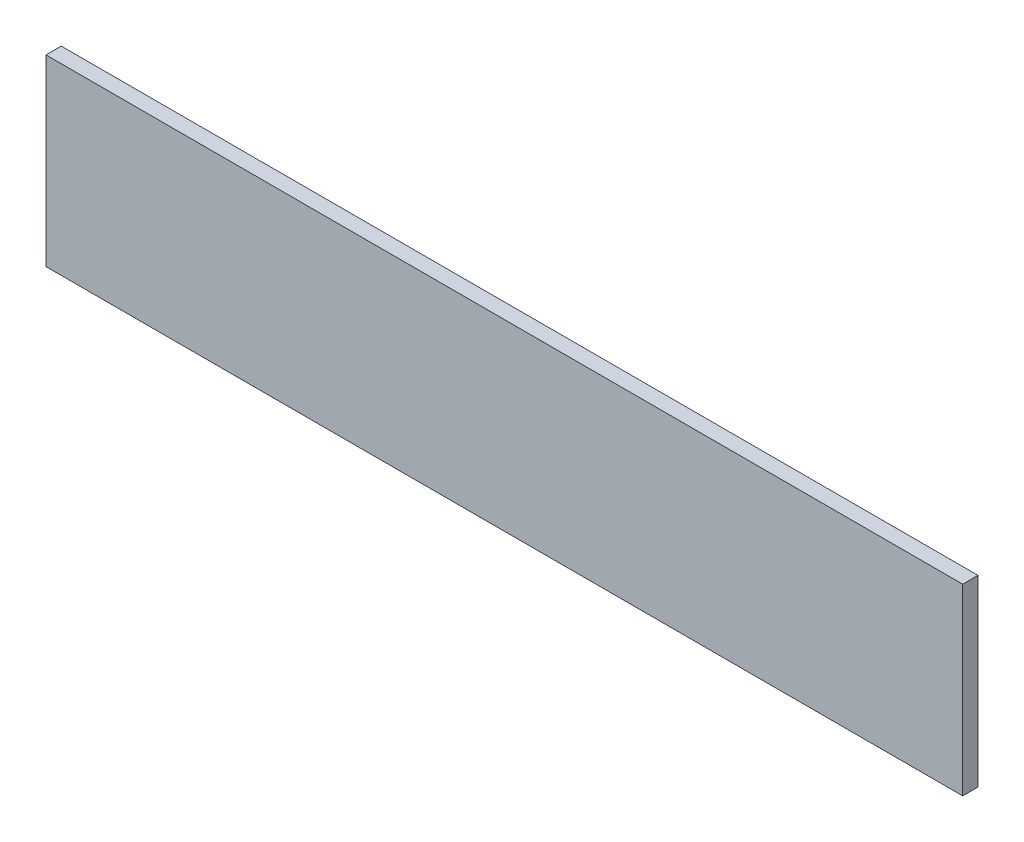
SolidWorks part; units mm, degrees
material "PVC 0.007 Plasticized"
ref_plane "Front Plane" through (0, 0, 0) normal (0, 0, 1) x (1, 0, 0)
ref_plane "Top Plane" through (0, 0, 0) normal (0, 1, 0) x (1, 0, 0)
ref_plane "Right Plane" through (0, 0, 0) normal (1, 0, 0) x (0, 0, -1)
sketch "Sketch1" plane through (0, 0, 0) normal (1, 0, 0) x (0, 0, -1)
  line L1 (-3.175, -38.1) -> (3.175, -38.1)
  line L2 (-3.175, -38.1) -> (-3.175, 38.1)
  line L3 (-3.175, 38.1) -> (3.175, 38.1)
  line L4 (3.175, -38.1) -> (3.175, 38.1)
  line L5 (-3.175, -38.1) -> (3.175, 38.1) construction
  line L6 (-3.175, 38.1) -> (3.175, -38.1) construction
  point P0 (0, 0)
  dimension "D1" = 76.2
  dimension "D2" = 6.35
extrude "Boss-Extrude1" add sketch "Sketch1" along normal blind 381
equation "\"D2@Sketch1\"=1in/4"
